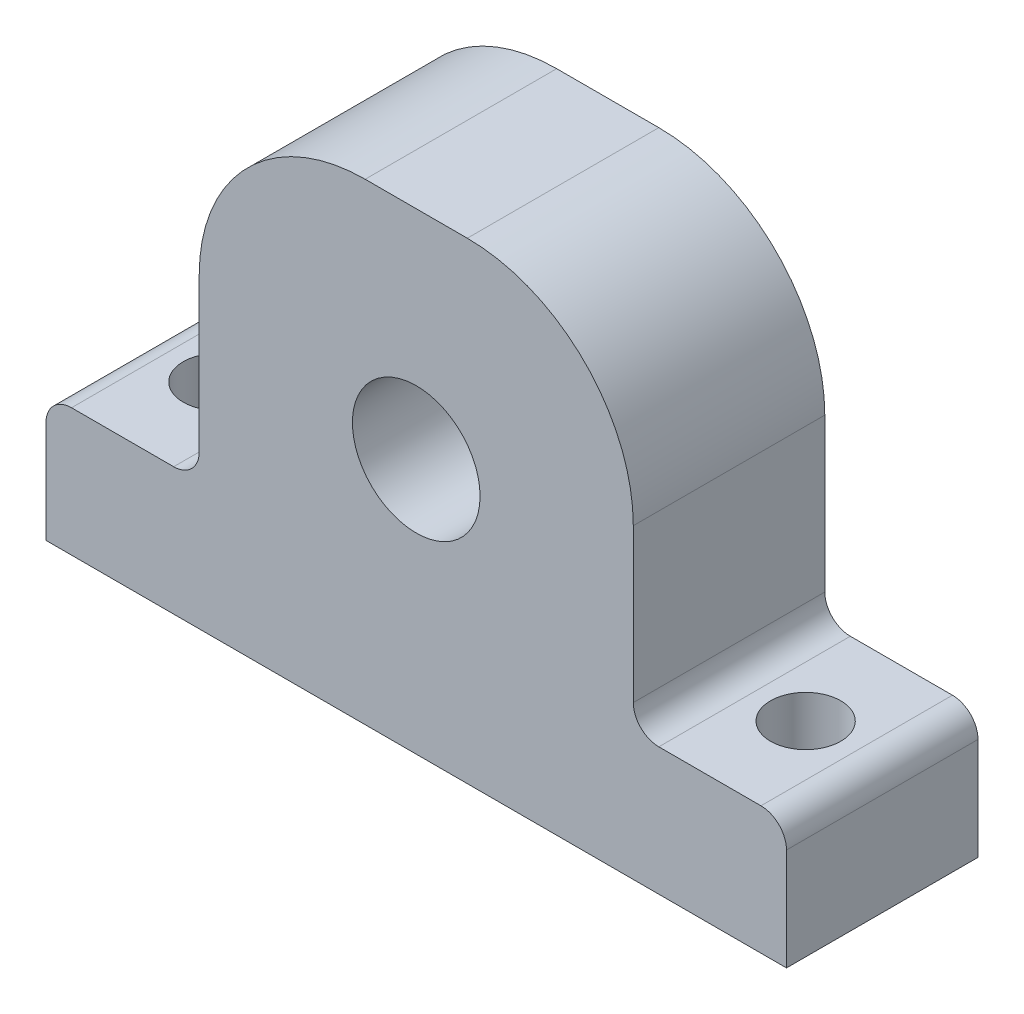
SolidWorks part; units mm, degrees
ref_plane "前视基准面" through (0, 0, 0) normal (0, 0, 1) x (1, 0, 0)
ref_plane "上视基准面" through (0, 0, 0) normal (0, 1, 0) x (1, 0, 0)
ref_plane "右视基准面" through (0, 0, 0) normal (1, 0, 0) x (0, 0, -1)
other "Configuration Table"
sketch "草图1" plane through (0, 0, 0) normal (0, 0, 1) x (1, 0, 0)
  line L0 (0, 18.5) -> (0, 5)
  line L1 (-29, 5) -> (29, 5)
  line L2 (-29, 5) -> (-29, -5)
  line L3 (-29, -5) -> (29, -5)
  line L4 (29, 5) -> (29, -5)
  line L5 (-29, 5) -> (29, -5) construction
  line L6 (-29, -5) -> (29, 5) construction
  line L7 (-17, 32) -> (17, 32)
  line L8 (-17, 32) -> (-17, 5)
  line L9 (-17, 5) -> (17, 5)
  line L10 (17, 32) -> (17, 5)
  line L11 (-17, 32) -> (17, 5) construction
  line L12 (-17, 5) -> (17, 32) construction
  line L13 (0, 5) -> (0, 0)
  line L14 (0, 15) -> (0, -5)
  circle A1 centre (0, 15) radius 5
  point P0 (0, 0)
  point P6 (0, 18.5)
  dimension "D7" = 10
  dimension "D1" = 58
  dimension "D2" = 10
  dimension "D3" = 34
  dimension "D4" = 20
  dimension "D5" = 27
extrude "凸台-拉伸1" add sketch "草图1" along normal blind 15
sketch "草图2" plane through (0, 5, 0) normal (0, 1, 0) x (1, 0, 0)
  line L0 (0, 0) -> (0, -15)
  line L1 (-17, -15) -> (17, -15) construction
  line L2 (-29, -15) -> (-17, -15) construction
  line L3 (17, -15) -> (29, -15) construction
  circle A0 centre (-23, -7.5) radius 2.75
  circle A1 centre (23, -7.5) radius 2.75
  dimension "D5" = 5.5
  dimension "D6" = 5.5
  dimension "D1" = 23
  dimension "D2" = 23
  dimension "D3" = 7.5
  dimension "D4" = 7.5
extrude "切除-拉伸1" cut sketch "草图2" against normal blind 15 contours A0 | A1
fillet "圆角2" radius 13 2 edges at (17, 32, 7.5) (-17, 32, 7.5)
fillet "圆角3" radius 2 4 edges at (-17, 5, 7.5) (17, 5, 7.5) (29, 5, 7.5) (-29, 5, 7.5)
